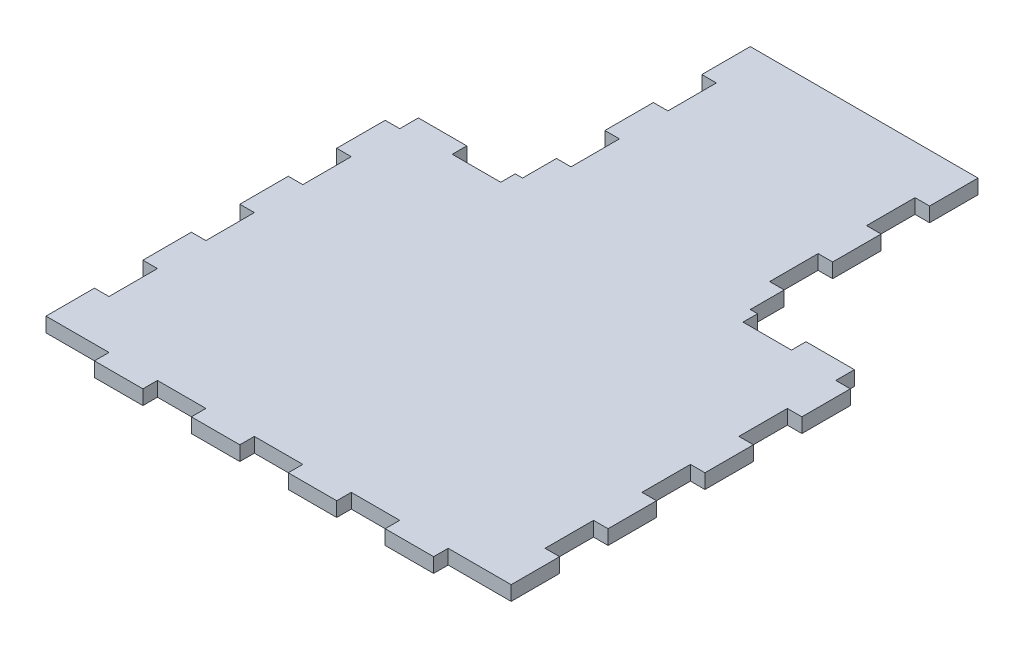
SolidWorks part; units mm, degrees
ref_plane "Front Plane" through (0, 0, 0) normal (0, 0, 1) x (1, 0, 0)
ref_plane "Top Plane" through (0, 0, 0) normal (0, 1, 0) x (1, 0, 0)
ref_plane "Right Plane" through (0, 0, 0) normal (1, 0, 0) x (0, 0, -1)
sketch "Sketch1" plane through (0, 0, 0) normal (0, 1, 0) x (1, 0, 0)
  line L0 (0, 60.8046) -> (0, -60.046) construction
  line L1 (20.5, 60.8046) -> (-20.5, 60.8046)
  line L2 (-20.5, 60.8046) -> (-20.5, 10.8046)
  line L3 (-20.5, 10.8046) -> (-45, 10.8046)
  line L4 (-45, 10.8046) -> (-45, -60.046)
  line L5 (-45, -60.046) -> (45, -60.046)
  line L6 (45, 10.8046) -> (45, -60.046)
  line L7 (20.5, 10.8046) -> (45, 10.8046)
  line L8 (20.5, 60.8046) -> (20.5, 10.8046)
  dimension "D1" = 41
  dimension "D2" = 50
  dimension "D3" = 90
extrude "Boss-Extrude1" add sketch "Sketch1" along normal blind 3
sketch "Sketch3" plane through (-20.5, 0, 0) normal (-1, 0, 0) x (0, 0, 1)
  line L0 (-60.8046, 0) -> (-10.8046, 0) construction
  line L1 (-60.8046, 3) -> (-50.8046, 3)
  line L2 (-60.8046, 3) -> (-60.8046, 0)
  line L3 (-60.8046, 0) -> (-50.8046, 0)
  line L4 (-50.8046, 3) -> (-50.8046, 0)
  line L5 (-60.8046, 3) -> (-50.8046, 0) construction
  line L6 (-60.8046, 0) -> (-50.8046, 3) construction
  point P4 (-55.8046, 1.5)
  dimension "D1" = 10
extrude "Boss-Extrude2" add sketch "Sketch3" along normal blind 3
pattern_linear "LPattern1" count 3 spacing 20 along (0, 0, 1) of "Boss-Extrude2"
ref_plane "Plane1" through (0, 0, 0) normal (-1, 0, 0) x (0, 0, 1)
sketch "Sketch4" plane through (0, 0, -10.8046) normal (0, 0, -1) x (-1, 0, 0)
  line L0 (-45, 0) -> (-20.5, 0) construction
  line L1 (-45, 3) -> (-35, 3)
  line L2 (-45, 3) -> (-45, 0)
  line L3 (-45, 0) -> (-35, 0)
  line L4 (-35, 3) -> (-35, 0)
  line L5 (-45, 3) -> (-35, 0) construction
  line L6 (-45, 0) -> (-35, 3) construction
  point P4 (-40, 1.5)
  dimension "D1" = 10
extrude "Boss-Extrude3" add sketch "Sketch4" along normal blind 3
pattern_linear "LPattern2" count 2 spacing 20 along (-1, 0, 0) of "Boss-Extrude3"
sketch "Sketch5" plane through (45, 0, 0) normal (1, 0, 0) x (0, 0, -1)
  line L0 (-60.046, 0) -> (13.8046, 0) construction
  line L1 (-60.046, 3) -> (-50.046, 3)
  line L2 (-60.046, 3) -> (-60.046, 0)
  line L3 (-60.046, 0) -> (-50.046, 0)
  line L4 (-50.046, 3) -> (-50.046, 0)
  line L5 (-60.046, 3) -> (-50.046, 0) construction
  line L6 (-60.046, 0) -> (-50.046, 3) construction
  point P4 (-55.046, 1.5)
  dimension "D1" = 10
extrude "Boss-Extrude4" add sketch "Sketch5" along normal blind 3
pattern_linear "LPattern3" count 4 spacing 20 along (0, 0, -1) of "Boss-Extrude4"
sketch "Sketch6" plane through (0, 0, 60.046) normal (0, 0, 1) x (1, 0, 0)
  line L0 (-45, 3) -> (48, 3) construction
  line L1 (5, 0) -> (15, 0)
  line L2 (5, 0) -> (5, 3)
  line L3 (5, 3) -> (15, 3)
  line L4 (15, 0) -> (15, 3)
  line L5 (5, 0) -> (15, 3) construction
  line L6 (5, 3) -> (15, 0) construction
  point P4 (10, 1.5)
  dimension "D1" = 10
  dimension "D2" = 5
extrude "Boss-Extrude5" add sketch "Sketch6" along normal blind 3
pattern_linear "LPattern4" count 2 spacing 20 along (1, 0, 0) of "Boss-Extrude5"
mirror "Mirror3" about plane through (0, 0, 0) normal (-1, 0, 0) of "LPattern2", "LPattern4", "LPattern3", "LPattern1", "Boss-Extrude2", "Boss-Extrude3", "Boss-Extrude4", "Boss-Extrude5"
